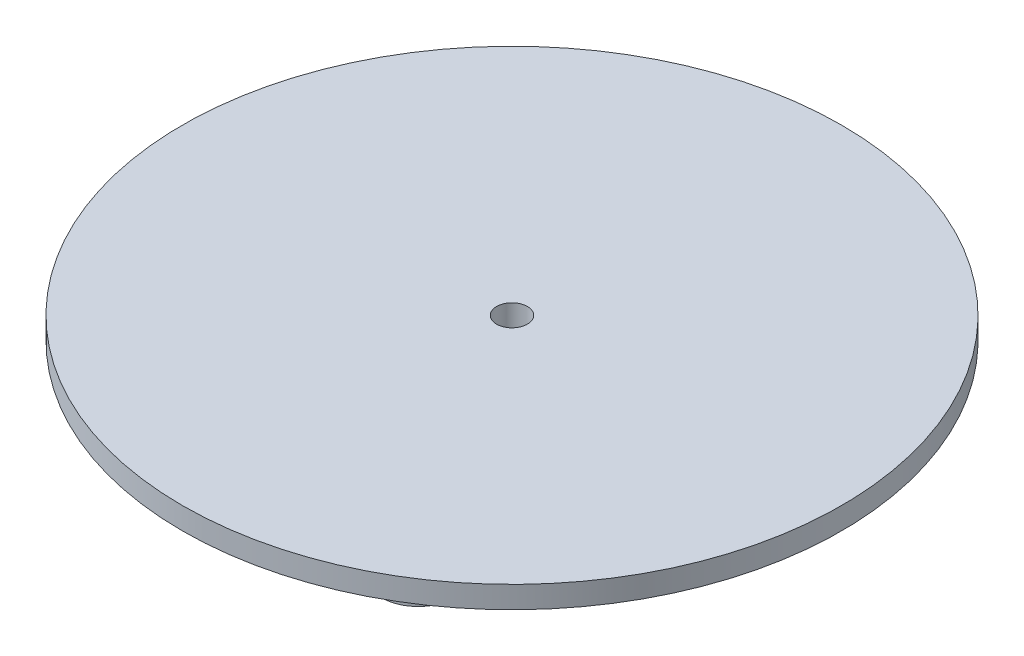
SolidWorks part; units mm, degrees
ref_plane "Plan de face" through (0, 0, 0) normal (0, 0, 1) x (1, 0, 0)
ref_plane "Plan de dessus" through (0, 0, 0) normal (0, 1, 0) x (1, 0, 0)
ref_plane "Plan de droite" through (0, 0, 0) normal (1, 0, 0) x (0, 0, -1)
sketch "Esquisse1" plane through (0, 0, 0) normal (0, 1, 0) x (1, 0, 0)
  circle A0 centre (0, 0) radius 45
  dimension "D1" = 90
extrude "Extrusion1" add sketch "Esquisse1" against normal blind 3
sketch "Esquisse2" plane through (0, -3, 0) normal (0, -1, 0) x (1, 0, 0)
  circle A0 centre (0, 0) radius 3.75
  circle A1 centre (0, 0) radius 6.75
  circle A2 centre (-35, 0) radius 5
  circle A3 centre (17.5, 30.3109) radius 5
  circle A4 centre (17.5, -30.3109) radius 5
  dimension "D1" = 7.5
  dimension "D3" = 10
  dimension "D2" = 3
extrude "Extrusion2" add sketch "Esquisse2" along normal blind 4
sketch "Esquisse3" plane through (0, 0, 0) normal (0, 1, 0) x (1, 0, 0)
  circle A0 centre (0, 0) radius 2.1
extrude "Enlèv. mat.-Extru.1" cut sketch "Esquisse3" against normal through all
